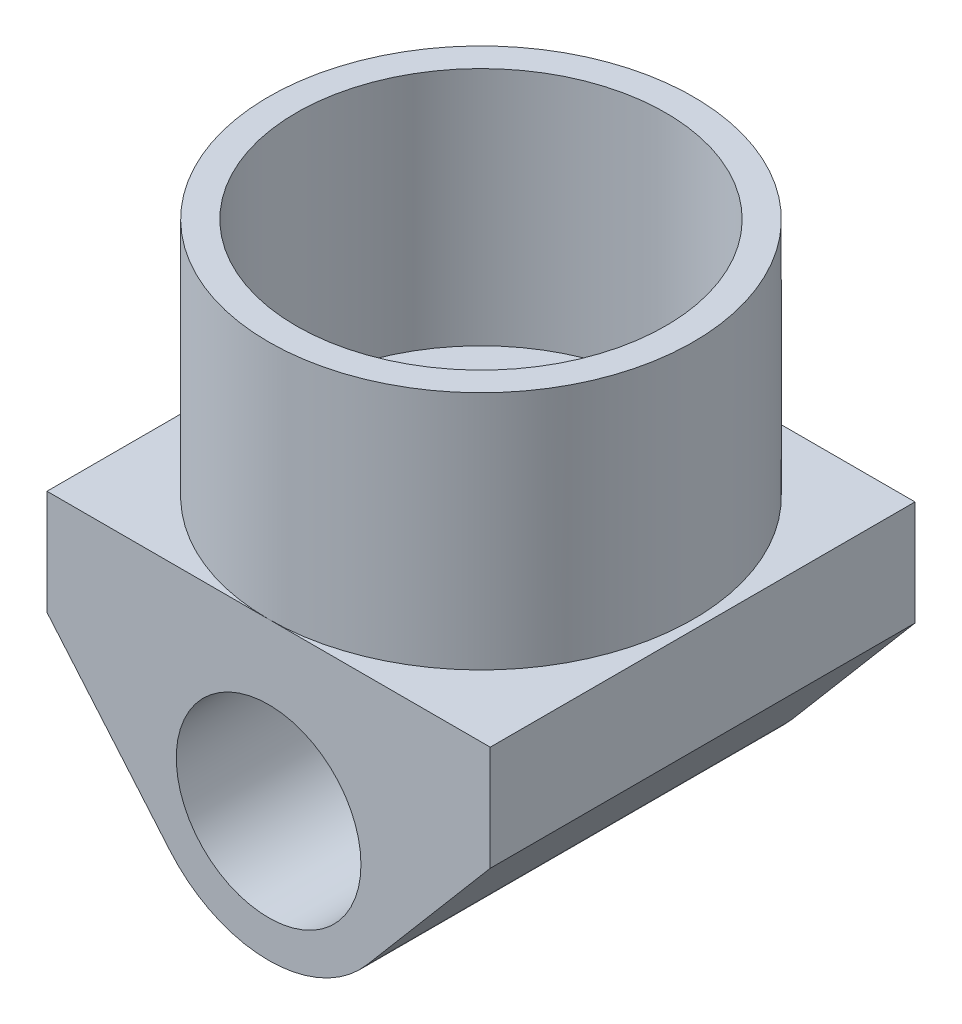
SolidWorks part; units mm, degrees
material "6061-T6 (SS)"
ref_plane "Front Plane" through (0, 0, 0) normal (0, 0, 1) x (1, 0, 0)
ref_plane "Top Plane" through (0, 0, 0) normal (0, 1, 0) x (1, 0, 0)
ref_plane "Right Plane" through (0, 0, 0) normal (1, 0, 0) x (0, 0, -1)
sketch "Sketch1" plane through (0, 0, 0) normal (0, 1, 0) x (1, 0, 0)
  circle A0 centre (0, 0) radius 29.21
  dimension "D1" = 58.42
extrude "Boss-Extrude1" add sketch "Sketch1" along normal blind 33.02
sketch "Sketch2" plane through (0, 0, 0) normal (0, -1, 0) x (1, 0, 0)
  line L1 (-30.48, 29.21) -> (30.48, 29.21)
  line L2 (-30.48, 29.21) -> (-30.48, -29.21)
  line L3 (-30.48, -29.21) -> (30.48, -29.21)
  line L4 (30.48, 29.21) -> (30.48, -29.21)
  point P4 (0, 29.21)
  point P6 (30.48, 0)
  dimension "D1" = 58.42
  dimension "D2" = 60.96
extrude "Boss-Extrude2" add sketch "Sketch2" along normal blind 40.64
sketch "Sketch3" plane through (0, 0, 29.21) normal (0, 0, 1) x (1, 0, 0)
  line L0 (30.48, 0) -> (0, 0) construction
  circle A0 centre (0, -22.86) radius 12.7
  dimension "D1" = 25.4
  dimension "D2" = 22.86
extrude "Cut-Extrude1" cut sketch "Sketch3" against normal through all
sketch "Sketch4" plane through (0, 33.02, 0) normal (0, 1, 0) x (1, 0, 0)
  circle A0 centre (0, 0) radius 25.4
  dimension "D1" = 50.8
extrude "Cut-Extrude2" cut sketch "Sketch4" against normal blind 33.02
sketch "Sketch5" plane through (0, 0, 29.21) normal (0, 0, 1) x (1, 0, 0)
  line L0 (13.5544, -34.3669) -> (30.48, -14.4295)
  line L1 (30.48, -40.64) -> (30.48, 0) construction
  line L2 (-13.5544, -34.3669) -> (-30.48, -14.4295)
  line L3 (-30.48, -40.64) -> (-30.48, 0) construction
  arc A0 (-13.5544, -34.3669) -> (13.5544, -34.3669) centre (0, -22.86) ccw
  dimension "D1" = 35.56
  dimension "D2" = 26.1529
extrude "Cut-Extrude3" cut sketch "Sketch5" against normal through all and the other way through all
